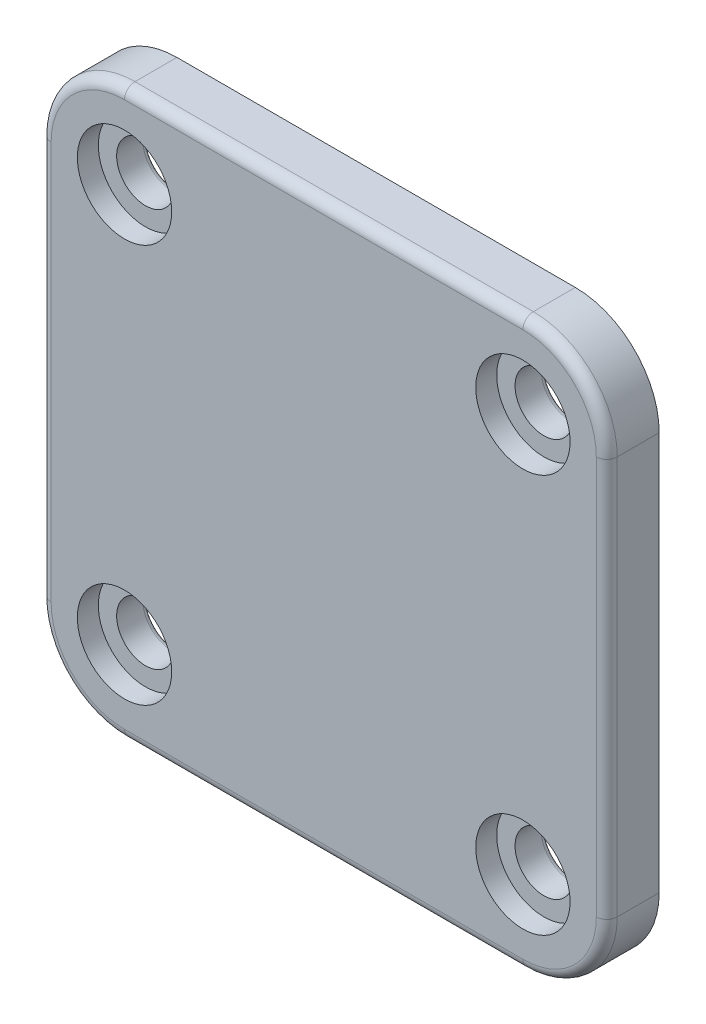
SolidWorks part; units mm, degrees
ref_plane "Спереди" through (0, 0, 0) normal (0, 0, 1) x (1, 0, 0)
ref_plane "Сверху" through (0, 0, 0) normal (0, 1, 0) x (1, 0, 0)
ref_plane "Справа" through (0, 0, 0) normal (1, 0, 0) x (0, 0, -1)
other "Configuration Table"
sketch "Sketch1" plane through (0, 0, 0) normal (0, 0, 1) x (1, 0, 0)
  line L1 (-19, -19) -> (19, -19) construction
  line L2 (-19, -19) -> (-19, 19) construction
  line L3 (-19, 19) -> (19, 19) construction
  line L4 (19, -19) -> (19, 19) construction
  line L5 (-19, -19) -> (19, 19) construction
  line L6 (-19, 19) -> (19, -19) construction
  line L7 (27, -27) -> (-27, -27)
  line L8 (27, -27) -> (27, 27)
  line L9 (27, 27) -> (-27, 27)
  line L10 (-27, -27) -> (-27, 27)
  line L11 (27, -27) -> (-27, 27) construction
  line L12 (27, 27) -> (-27, -27) construction
  circle A0 centre (-19, 19) radius 2.75
  circle A1 centre (19, 19) radius 2.75
  circle A2 centre (19, -19) radius 2.75
  circle A3 centre (-19, -19) radius 2.75
  point P0 (0, 0)
  point P10 (0, 0)
  dimension "D3" = 5.5
  dimension "D1" = 38
  dimension "D2" = 38
  dimension "D4" = 8
  dimension "D5" = 8
extrude "Boss-Extrude1" add sketch "Sketch1" along normal blind 5
fillet "Fillet1" radius 8 4 edges at (-27, 27, 2.5) (27, -27, 2.5) (-27, -27, 2.5) (27, 27, 2.5)
fillet "Fillet2" radius 0.5 8 edges at (21.75, -19, 0) (21.75, 19, 0) (-16.25, 19, 0) (-16.25, -19, 0) (-16.25, -19, 5) (21.75, -19, 5) (21.75, 19, 5) (-16.25, 19, 5)
fillet "Fillet3" radius 1 8 edges at (-24.6569, 24.6569, 5) (0, 27, 5) (24.6569, 24.6569, 5) (27, 0, 5) (24.6569, -24.6569, 5) (0, -27, 5) (-24.6569, -24.6569, 5) (-27, 0, 5)
sketch "Sketch2" plane through (0, 0, 5) normal (0, 0, 1) x (1, 0, 0)
  circle A0 centre (-19, 19) radius 4.5
  circle A1 centre (19, 19) radius 4.5
  circle A2 centre (19, -19) radius 4.5
  circle A3 centre (-19, -19) radius 4.5
  dimension "D1" = 9
extrude "Cut-Extrude2" cut sketch "Sketch2" against normal offset from surface (2 mm away) 3 up to face at (22.25, -19, 0)
